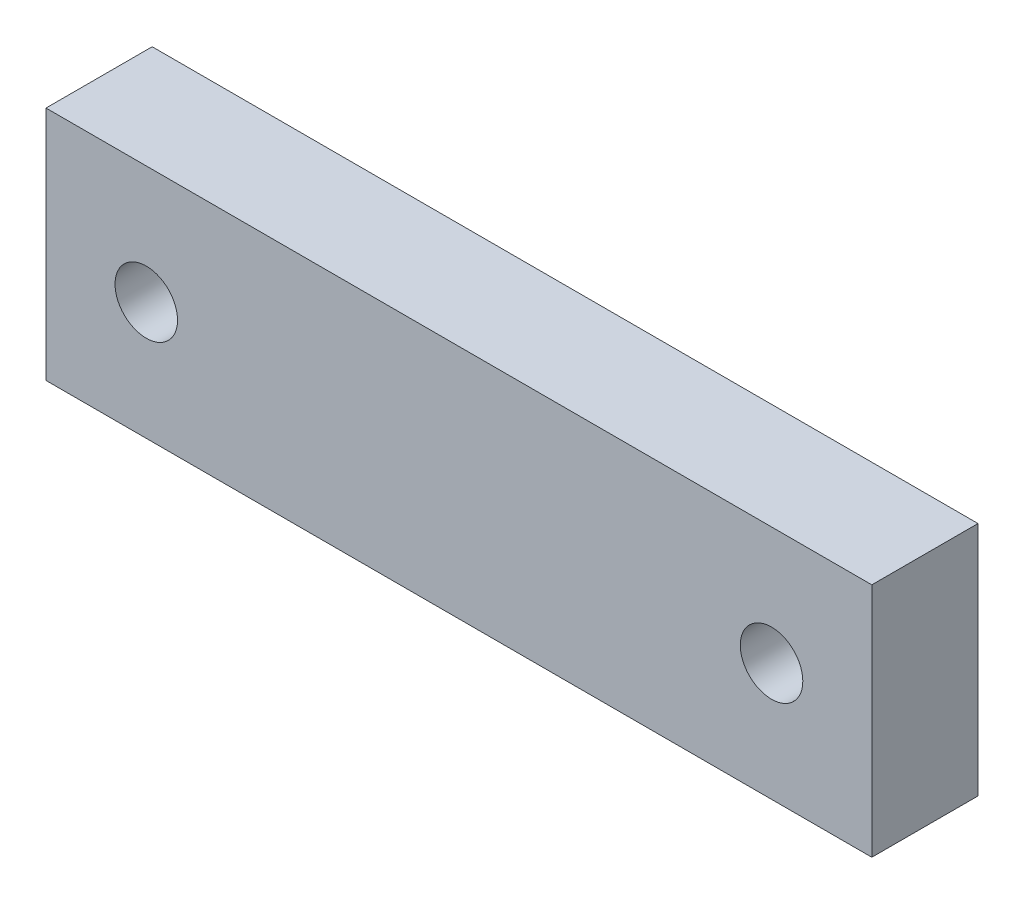
SolidWorks part; units mm, degrees
material "ABS"
ref_plane "Front Plane" through (0, 0, 0) normal (0, 0, 1) x (1, 0, 0)
ref_plane "Top Plane" through (0, 0, 0) normal (0, 1, 0) x (1, 0, 0)
ref_plane "Right Plane" through (0, 0, 0) normal (1, 0, 0) x (0, 0, -1)
sketch "Sketch1" plane through (0, 0, 0) normal (0, 0, 1) x (1, 0, 0)
  line L0 (75, -42.5) -> (-75, -42.5) construction
  line L1 (-35, -42.5) -> (35, -42.5)
  line L2 (-35, -42.5) -> (-35, -62.5)
  line L3 (-35, -62.5) -> (35, -62.5)
  line L4 (35, -42.5) -> (35, -62.5)
  line L5 (95, -62.5) -> (-95, -62.5) construction
  line L8 (-45, -62.5) -> (-45, -42.5) construction
  line L9 (45, -42.5) -> (45, -62.5) construction
  circle A0 centre (26.5, -52.5) radius 2.65 construction
  circle A1 centre (-26.5, -52.5) radius 2.65 construction
  circle A2 centre (26.5, -52.5) radius 2.65
  circle A3 centre (-26.5, -52.5) radius 2.65
  dimension "D1" = 10
  dimension "D2" = 10
extrude "Extrude1" add sketch "Sketch1" along normal blind 9
